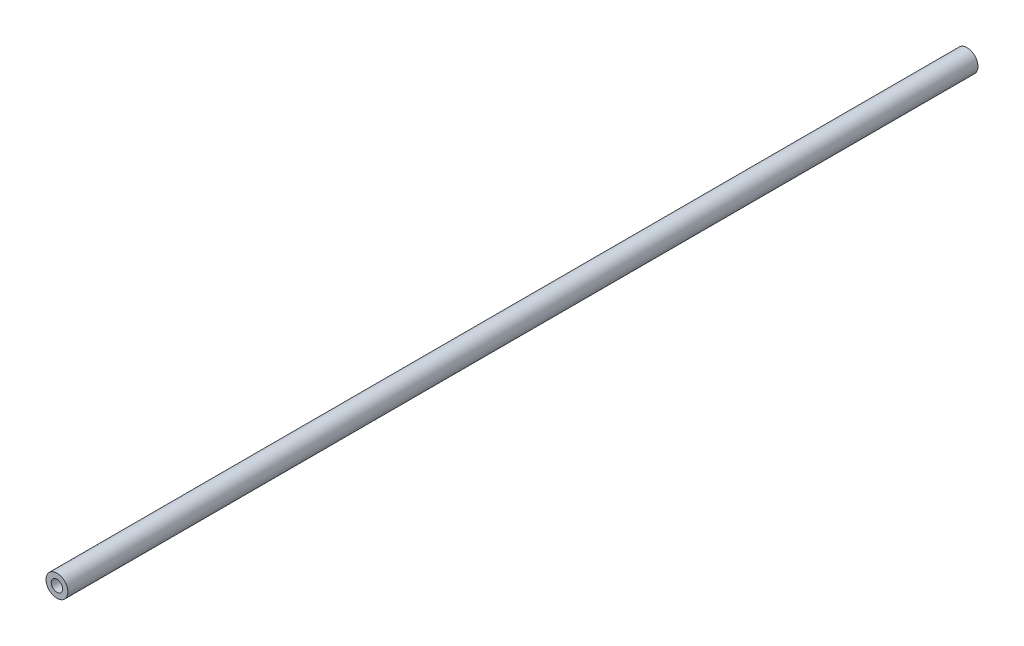
SolidWorks part; units mm, degrees
ref_plane "Front Plane" through (0, 0, 0) normal (0, 0, 1) x (1, 0, 0)
ref_plane "Top Plane" through (0, 0, 0) normal (0, 1, 0) x (1, 0, 0)
ref_plane "Right Plane" through (0, 0, 0) normal (1, 0, 0) x (0, 0, -1)
sketch "Sketch1" plane through (0, 0, 0) normal (0, 0, 1) x (1, 0, 0)
  circle A0 centre (0, 0) radius 3.175
  circle A1 centre (0, 0) radius 6.096
  dimension "D1" = 6.35
  dimension "D2" = 12.192
extrude "Boss-Extrude1" add sketch "Sketch1" along normal blind 508
